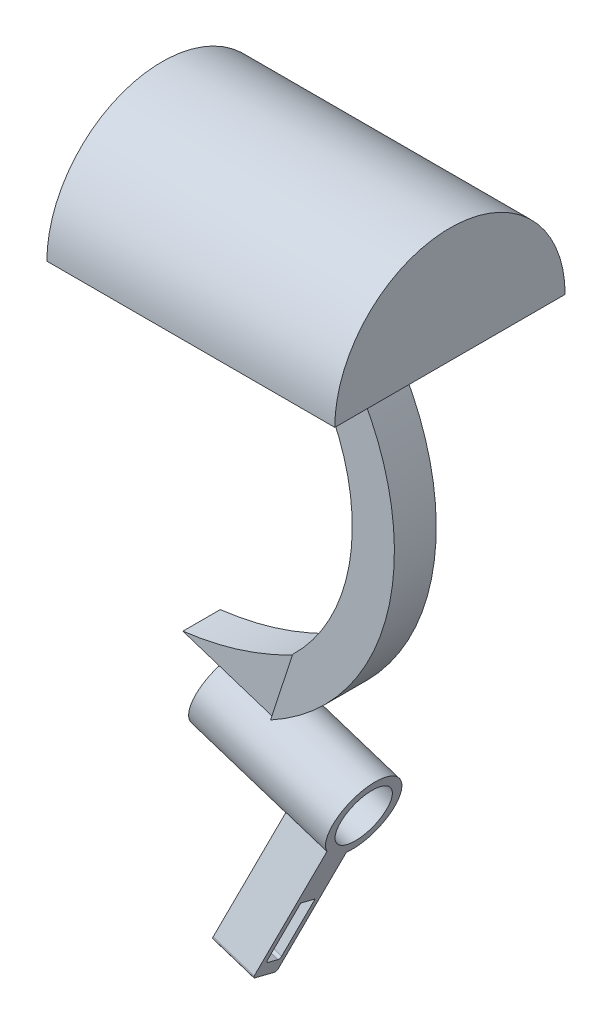
SolidWorks part; units mm, degrees
ref_plane "Front Plane" through (0, 0, 0) normal (0, 0, 1) x (1, 0, 0)
ref_plane "Top Plane" through (0, 0, 0) normal (0, 1, 0) x (1, 0, 0)
ref_plane "Right Plane" through (0, 0, 0) normal (1, 0, 0) x (0, 0, -1)
sketch "Sketch1" plane through (0, 0, 0) normal (0, 1, 0) x (1, 0, 0)
  line L1 (0, 0.371) -> (25.4, 0.371)
  line L2 (0, 0.371) -> (0, 10.531)
  line L3 (0, 10.531) -> (25.4, 10.531)
  line L4 (25.4, 0.371) -> (25.4, 10.531)
  dimension "D1" = 25.4
  dimension "D2" = 10.16
revolve "Revolve1" add sketch "Sketch1" angle 180 about L1
sketch "Sketch4" plane through (0, 0, 0) normal (0, 1, 0) x (1, 0, 0)
  line L0 (12.7, -9.789) -> (12.7, 10.531) construction
  line L1 (25.4, -9.789) -> (0, -9.789) construction
  line L2 (25.4, 10.531) -> (0, 10.531) construction
  line L3 (0, 0.371) -> (25.4, 0.371) construction
  line L4 (0, -9.789) -> (0, 10.531) construction
  line L5 (25.4, 10.531) -> (25.4, -9.789) construction
  line L7 (9.555, 2.216) -> (15.845, 2.216)
  line L8 (9.555, 2.216) -> (9.555, -1.474)
  line L9 (9.555, -1.474) -> (15.845, -1.474)
  line L10 (15.845, 2.216) -> (15.845, -1.474)
  line L11 (9.555, 2.216) -> (15.845, -1.474) construction
  line L12 (9.555, -1.474) -> (15.845, 2.216) construction
  point P12 (12.7, 0.371)
  dimension "D1" = 6.29
  dimension "D2" = 3.69
sketch "Sketch5" plane through (0, 0, 0) normal (0, 0, 1) x (1, 0, 0)
  line L0 (12.7, 0) -> (12.7, -28.9) construction
  line L1 (9.555, 0) -> (15.845, 0) construction
  arc A0 (12.7, 0) -> (12.3926, -30.5071) centre (1.4568, -15.1418) cw
  dimension "D1" = 28.9
sweep "Sweep1" add profiles "Sketch4" path "Sketch5"
ref_plane "Plane2" through (20.1643, -6.5381, 0) normal (-0.9512, 0.3084, 0) x (0, 0, 1)
sketch "Sketch6" plane through (20.1643, -6.5381, 0) normal (-0.9512, 0.3084, 0) x (0, 0, 1)
  line L1 (1.2864, -22.2174) -> (-2.0086, -22.2174)
  line L2 (1.2864, -22.2174) -> (1.2864, -28.1924)
  line L3 (1.2864, -28.1924) -> (-2.0086, -28.1924)
  line L4 (-2.0086, -22.2174) -> (-2.0086, -28.1924)
  line L5 (1.2864, -22.2174) -> (-2.0086, -28.1924) construction
  line L6 (1.2864, -28.1924) -> (-2.0086, -22.2174) construction
  point P0 (-0.3611, -25.2049)
extrude "Boss-Extrude1" add sketch "Sketch6" along normal blind 5.08
ref_plane "Plane3" through (15.332, -4.9713, 0) normal (-0.9512, 0.3084, 0) x (0, 0, 1)
sketch "Sketch7" plane through (15.332, -4.9713, 0) normal (-0.9512, 0.3084, 0) x (0, 0, 1)
  line L0 (-0.3611, -22.2174) -> (-0.3611, -30.7339) construction
  line L1 (1.2864, -22.2174) -> (-2.0086, -22.2174) construction
  line L2 (-2.0086, -28.1924) -> (1.2864, -28.1924) construction
  circle A0 centre (-0.3611, -31.161) radius 3.22
  point P8 (-0.3611, -28.1924)
  dimension "D1" = 2.9686
extrude "Boss-Extrude7" add sketch "Sketch7" against normal blind 12.7
sketch "Sketch9" plane through (15.332, -4.9713, 0) normal (-0.9512, 0.3084, 0) x (0, 0, 1)
  line L1 (1.2864, -28.1924) -> (-2.0086, -28.1924)
  line L2 (1.2864, -28.1924) -> (1.2864, -22.2174)
  line L3 (1.2864, -22.2174) -> (-2.0086, -22.2174)
  line L4 (-2.0086, -28.1924) -> (-2.0086, -22.2174)
extrude "Boss-Extrude8" add sketch "Sketch9" along normal blind 3.302
sketch "Sketch10" plane through (0, 0, 0) normal (0, 0, 1) x (1, 0, 0)
  line L0 (3.4955, -30.7707) -> (5.3384, -25.0871)
  line L1 (5.3384, -25.0871) -> (13.3117, -27.6723)
  spline S0 degree 2 poles (13.3117, -27.6723) (8.6837, -30.1294) (3.4955, -30.7707) knots 0 0 0 1 1 1
extrude "Cut-Extrude1" cut sketch "Sketch10" against normal blind 3.302 and the other way blind 3.302
ref_plane "Plane6" through (27.4128, -8.8884, 0) normal (0.9512, -0.3084, 0) x (0, 0, -1)
sketch "Sketch11" plane through (27.4128, -8.8884, 0) normal (0.9512, -0.3084, 0) x (0, 0, -1)
  line L0 (0.4223, -27.8725) -> (0.3611, -34.381) construction
  line L1 (-2.8589, -31.161) -> (3.5811, -31.161) construction
  circle A0 centre (0.3611, -31.161) radius 3.22 construction
  circle A1 centre (0.3917, -31.1268) radius 2.375
  dimension "D1" = 4.75
extrude "Cut-Extrude2" cut sketch "Sketch11" against normal blind 12.446 and the other way blind 2.54
sketch "Sketch13" plane through (27.4128, -8.8884, 0) normal (0.9512, -0.3084, 0) x (0, 0, -1)
  line L0 (-0.1893, -34.3336) -> (-3.3746, -43.5144)
  line L1 (-3.6655, -43.6555) -> (-5.5954, -42.9859)
  line L2 (-5.7365, -42.695) -> (-2.3419, -32.9109)
  line L3 (-2.3419, -32.9109) -> (-0.1893, -34.3336)
  line L8 (-3.4623, -42.2419) -> (-1.8983, -37.7341)
  line L9 (-1.8983, -37.7341) -> (-3.3155, -37.2424)
  line L10 (-3.3155, -37.2424) -> (-4.8794, -41.7502)
  line L11 (-4.7384, -42.0411) -> (-3.7532, -42.3829)
  line L12 (-2.6803, -39.988) -> (-2.2079, -40.1519)
  line L13 (-4.0974, -39.4963) -> (-4.5698, -39.3324)
  circle A0 centre (0.3611, -31.161) radius 3.22 construction
  arc A1 (-3.4623, -42.2419) -> (-3.7532, -42.3829) centre (-3.6783, -42.1669) cw
  arc A2 (-4.8794, -41.7502) -> (-4.7384, -42.0411) centre (-4.6635, -41.8251) ccw
  arc A3 (-5.5954, -42.9859) -> (-5.7365, -42.695) centre (-5.5205, -42.7699) cw
  arc A4 (-3.3746, -43.5144) -> (-3.6655, -43.6555) centre (-3.5905, -43.4395) cw
  point P16 (-3.5372, -42.4579)
  point P19 (-4.9544, -41.9662)
  point P22 (-5.8114, -42.9109)
  point P25 (-3.4495, -43.7304)
  dimension "D6" = 0.2286
  dimension "D1" = 2.5
  dimension "D2" = 10
  dimension "D3" = 1.5
  dimension "D4" = 5
  dimension "D5" = 4.7238
extrude "Boss-Extrude11" add sketch "Sketch13" against normal blind 3.81 contours L13 L10 L9 L8 L12 L0 L3 L2 | A4 L0 L12 L8 A1 L11 A2 L10 L13 L2 A3 L1
sketch "Sketch14" plane through (27.4128, -8.8884, 0) normal (0.9512, -0.3084, 0) x (0, 0, -1)
  circle A0 centre (0.3611, -31.161) radius 2.4209
extrude "Cut-Extrude3" cut sketch "Sketch14" against normal blind 22.606
